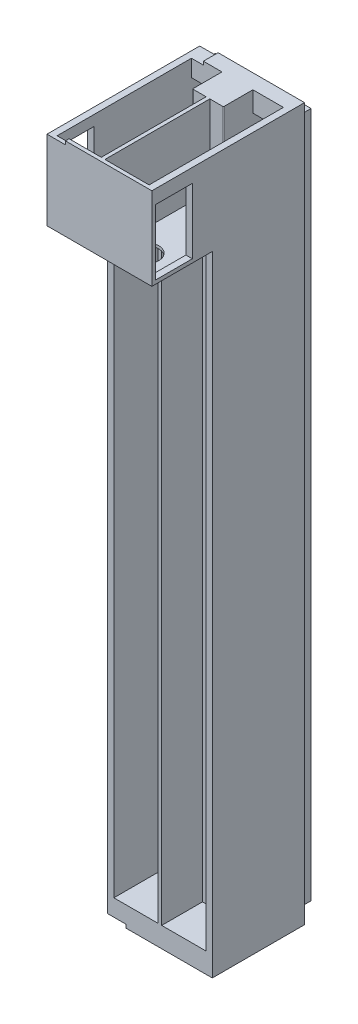
SolidWorks part; units mm, degrees
material "ABS"
ref_plane "Płaszczyzna przednia" through (0, 0, 0) normal (0, 0, 1) x (1, 0, 0)
ref_plane "Płaszczyzna górna" through (0, 0, 0) normal (0, 1, 0) x (1, 0, 0)
ref_plane "Płaszczyzna prawa" through (0, 0, 0) normal (1, 0, 0) x (0, 0, -1)
sketch "Szkic1" plane through (0, 0, 0) normal (0, 0, 1) x (1, 0, 0)
  line L0 (-90.4269, 49.2609) -> (-90.4269, -315.7391)
  line L1 (-91.9269, 53.7609) -> (-38.9269, 53.7609)
  line L2 (-91.9269, 53.7609) -> (-91.9269, -320.2391)
  line L3 (-91.9269, -320.2391) -> (-38.9269, -320.2391)
  line L4 (-38.9269, 53.7609) -> (-38.9269, -320.2391)
  line L5 (-40.4269, 49.2609) -> (-64.4269, 49.2609)
  line L6 (-90.4269, -315.7391) -> (-66.4269, -315.7391)
  line L7 (-90.4269, 49.2609) -> (-66.4269, 49.2609)
  line L8 (-66.4269, 49.2609) -> (-66.4269, -315.7391)
  line L10 (-64.4269, 49.2609) -> (-64.4269, -315.7391)
  line L13 (-40.4269, 49.2609) -> (-40.4269, -315.7391)
  line L14 (-40.4269, -315.7391) -> (-64.4269, -315.7391)
  dimension "D1" = 374
  dimension "D2" = 24
  dimension "D3" = 53
  dimension "D4" = 365
extrude "Dodanie-wyciągnięcie2" add sketch "Szkic1" along normal blind 12 contours L3 L4 L1 L2 | L6 L8 L7 L0 | L14 L10 L5 L13
sketch "Szkic2" plane through (-66.4269, 0, 0) normal (-1, 0, 0) x (0, 0, 1)
  line L0 (12, 49.2609) -> (12, -315.7391) construction
  line L1 (0, 49.2609) -> (12, 49.2609)
  line L2 (0, 49.2609) -> (0, 45.7609)
  line L3 (0, 45.7609) -> (12, 45.7609)
  line L4 (12, 49.2609) -> (12, 45.7609)
extrude "Wytnij-wyciągnięcie1" cut sketch "Szkic2" against normal blind 2
ref_plane "Płaszczyzna1" through (0, 0, 12) normal (0, 0, 1) x (1, 0, 0)
sketch "Szkic3" plane through (0, 0, 12) normal (0, 0, 1) x (1, 0, 0)
  line L6 (-38.9269, -320.2391) -> (-91.9269, -320.2391)
  line L7 (-38.9269, -320.2391) -> (-38.9269, 53.7609)
  line L8 (-38.9269, 53.7609) -> (-91.9269, 53.7609)
  line L9 (-91.9269, -320.2391) -> (-91.9269, 53.7609)
extrude "Dodanie-wyciągnięcie3" add sketch "Szkic3" along normal blind 2
sketch "Szkic4" plane through (0, 0, 14) normal (0, 0, 1) x (1, 0, 0)
  line L64 (-46.9269, -11.0391) -> (-56.3269, -11.0391)
  line L69 (-90.4269, 49.2609) -> (-40.4269, 49.2609) construction
  line L70 (-53.7269, 49.2609) -> (-40.4269, 49.2609)
  line L71 (-40.4269, 49.2609) -> (-40.4269, 18.7608)
  line L72 (-40.4269, 49.2609) -> (-40.4269, -315.7391) construction
  line L73 (-40.4269, 18.7608) -> (-53.7269, 18.7608)
  line L74 (-53.7269, 49.2609) -> (-53.7269, 18.7608)
  line L77 (-77.1269, 49.2609) -> (-77.1269, 18.7608)
  line L78 (-90.4269, 18.7608) -> (-77.1269, 18.7608)
  line L79 (-90.4269, 49.2609) -> (-90.4269, 18.7608)
  line L80 (-77.1269, 49.2609) -> (-90.4269, 49.2609)
  line L81 (-74.5269, -35.3991) -> (-74.5269, -40.4791)
  line L82 (-74.5269, -40.4791) -> (-83.9269, -40.4791)
  line L87 (-46.9269, -35.3991) -> (-46.9269, -11.0391)
  line L89 (-56.3269, -35.3991) -> (-56.3269, -11.0391)
  line L90 (-74.5269, -35.3991) -> (-74.5269, -11.0391)
  line L92 (-83.9269, -35.3991) -> (-83.9269, -11.0391)
  line L93 (-83.9269, -11.0391) -> (-74.5269, -11.0391)
  line L94 (-46.9269, -101.2391) -> (-46.9269, -166.1991)
  line L95 (-46.9269, -166.1991) -> (-56.3269, -166.1991)
  line L96 (-46.9269, -101.2391) -> (-56.3269, -101.2391)
  line L97 (-56.3269, -166.1991) -> (-56.3269, -101.2391)
  line L98 (-74.5269, -166.1991) -> (-74.5269, -101.2391)
  line L99 (-83.9269, -101.2391) -> (-74.5269, -101.2391)
  line L100 (-83.9269, -166.1991) -> (-74.5269, -166.1991)
  line L101 (-83.9269, -101.2391) -> (-83.9269, -166.1991)
  line L102 (-83.9269, -40.4791) -> (-83.9269, -35.3991)
  line L103 (-56.3269, -35.3991) -> (-56.3269, -40.4791)
  line L104 (-56.3269, -40.4791) -> (-46.9269, -40.4791)
  line L105 (-46.9269, -40.4791) -> (-46.9269, -35.3991)
extrude "Wytnij-wyciągnięcie2" cut sketch "Szkic4" against normal blind 2
sketch "Szkic5" plane through (0, 0, 14) normal (0, 0, 1) x (1, 0, 0)
  line L1 (-91.9269, -320.2391) -> (-38.9269, -320.2391) construction
  line L7 (-64.4269, -320.2391) -> (-66.4269, -320.2391)
  line L11 (-64.4269, -320.2391) -> (-64.4269, 53.7609)
  line L12 (-64.4269, 53.7609) -> (-66.4269, 53.7609)
  line L13 (-66.4269, -320.2391) -> (-66.4269, 53.7609)
extrude "Dodanie-wyciągnięcie4" add sketch "Szkic5" along normal blind 43
sketch "Szkic6" plane through (0, 0, 14) normal (0, 0, 1) x (1, 0, 0)
  line L0 (-64.4269, 16.7608) -> (-40.4269, 16.7608)
  line L4 (-64.4269, -320.2391) -> (-64.4269, 53.7609) construction
  line L5 (-40.4269, 49.2609) -> (-40.4269, -315.7391) construction
  line L6 (-40.4269, 16.7608) -> (-40.4269, 53.7609)
  line L7 (-91.9269, 53.7609) -> (-38.9269, 53.7609) construction
  line L8 (-40.4269, 53.7609) -> (-38.9269, 53.7609)
  line L19 (-90.4269, 53.7609) -> (-91.9269, 53.7609)
  line L20 (-90.4269, 16.7608) -> (-90.4269, 53.7609)
  line L21 (-66.4269, 16.7608) -> (-90.4269, 16.7608)
  line L22 (-64.4269, 16.7608) -> (-64.4269, 15.2608)
  line L23 (-64.4269, 15.2608) -> (-38.9269, 15.2608)
  line L24 (-38.9269, 15.2608) -> (-38.9269, 53.7609)
  line L25 (-91.9269, 15.2608) -> (-91.9269, 53.7609)
  line L26 (-66.4269, 15.2608) -> (-91.9269, 15.2608)
  line L27 (-66.4269, 16.7608) -> (-66.4269, 15.2608)
extrude "Dodanie-wyciągnięcie5" add sketch "Szkic6" along normal blind 41.5
ref_plane "Płaszczyzna2" through (0, 0, 55.5) normal (0, 0, 1) x (1, 0, 0)
sketch "Szkic7" plane through (0, 0, 55.5) normal (0, 0, 1) x (1, 0, 0)
  line L1 (-38.9269, 15.2608) -> (-64.4269, 15.2608)
  line L2 (-38.9269, 15.2608) -> (-38.9269, 53.7609)
  line L3 (-38.9269, 53.7609) -> (-64.4269, 53.7609)
  line L4 (-64.4269, 15.2608) -> (-64.4269, 53.7609)
  line L5 (-66.4269, 15.2608) -> (-91.9269, 15.2608)
  line L6 (-66.4269, 15.2608) -> (-66.4269, 53.7609)
  line L7 (-66.4269, 53.7609) -> (-91.9269, 53.7609)
  line L8 (-91.9269, 15.2608) -> (-91.9269, 53.7609)
extrude "Dodanie-wyciągnięcie6" add sketch "Szkic7" along normal blind 1.5
sketch "Szkic10" plane through (0, 0, 14) normal (0, 0, 1) x (1, 0, 0)
  line L0 (-91.9269, 15.2608) -> (-91.9269, -320.2391)
  line L1 (-91.9269, -320.2391) -> (-66.4269, -320.2391)
  line L2 (-66.4269, -320.2391) -> (-66.4269, -315.7391)
  line L3 (-66.4269, 15.2608) -> (-66.4269, -320.2391) construction
  line L4 (-66.4269, -315.7391) -> (-90.4269, -315.7391)
  line L5 (-90.4269, -315.7391) -> (-90.4269, 15.2608)
  line L6 (-91.9269, 15.2608) -> (-66.4269, 15.2608) construction
  line L7 (-90.4269, 15.2608) -> (-91.9269, 15.2608)
  dimension "D1" = 24
  dimension "D2" = 330.9999
extrude "Dodanie-wyciągnięcie7" add sketch "Szkic10" along normal blind 43
sketch "Szkic11" plane through (0, 0, 14) normal (0, 0, 1) x (1, 0, 0)
  line L0 (-38.9269, 15.2608) -> (-38.9269, -320.2391)
  line L1 (-38.9269, -320.2391) -> (-64.4269, -320.2391)
  line L2 (-64.4269, -320.2391) -> (-64.4269, -315.7391)
  line L3 (-64.4269, -320.2391) -> (-64.4269, 15.2608) construction
  line L4 (-64.4269, -315.7391) -> (-40.4269, -315.7391)
  line L5 (-40.4269, -315.7391) -> (-40.4269, 15.2608)
  line L6 (-64.4269, 15.2608) -> (-38.9269, 15.2608) construction
  line L7 (-40.4269, 15.2608) -> (-38.9269, 15.2608)
  dimension "D1" = 330.9999
  dimension "D2" = 24
extrude "Dodanie-wyciągnięcie8" add sketch "Szkic11" along normal blind 43
sketch "Szkic15" plane through (-91.9269, 0, 0) normal (-1, 0, 0) x (0, 0, 1)
  line L1 (57, 53.7609) -> (0, 53.7609)
  line L2 (57, 53.7609) -> (57, -320.2391)
  line L3 (57, -320.2391) -> (0, -320.2391)
  line L4 (0, 53.7609) -> (0, -320.2391)
extrude "Dodanie-wyciągnięcie10" add sketch "Szkic15" along normal blind 1
sketch "Szkic16" plane through (-38.9269, 0, 0) normal (1, 0, 0) x (0, 0, -1)
  line L1 (-57, -320.2391) -> (0, -320.2391)
  line L2 (-57, -320.2391) -> (-57, 53.7609)
  line L3 (-57, 53.7609) -> (0, 53.7609)
  line L4 (0, -320.2391) -> (0, 53.7609)
extrude "Dodanie-wyciągnięcie11" add sketch "Szkic16" along normal blind 1
sketch "Szkic17" plane through (0, 53.7609, 0) normal (0, 1, 0) x (1, 0, 0)
  line L1 (-37.9269, -57) -> (-92.9269, -57)
  line L2 (-37.9269, -57) -> (-37.9269, 0)
  line L3 (-37.9269, 0) -> (-92.9269, 0)
  line L4 (-92.9269, -57) -> (-92.9269, 0)
  line L5 (-40.4269, -55.5) -> (-64.4269, -55.5)
  line L6 (-40.4269, -55.5) -> (-40.4269, -14)
  line L7 (-40.4269, -14) -> (-64.4269, -14)
  line L8 (-64.4269, -55.5) -> (-64.4269, -14)
  line L9 (-66.4269, -55.5) -> (-90.4269, -55.5)
  line L10 (-66.4269, -55.5) -> (-66.4269, -14)
  line L11 (-66.4269, -14) -> (-90.4269, -14)
  line L12 (-90.4269, -55.5) -> (-90.4269, -14)
extrude "Dodanie-wyciągnięcie12" add sketch "Szkic17" along normal blind 1
sketch "Szkic18" plane through (0, -320.2391, 0) normal (0, -1, 0) x (1, 0, 0)
  line L1 (-92.9269, 57) -> (-37.9269, 57)
  line L2 (-92.9269, 57) -> (-92.9269, 0)
  line L3 (-92.9269, 0) -> (-37.9269, 0)
  line L4 (-37.9269, 57) -> (-37.9269, 0)
extrude "Dodanie-wyciągnięcie13" add sketch "Szkic18" along normal blind 1
sketch "Szkic19" plane through (0, 0, 0) normal (0, 0, -1) x (-1, 0, 0)
  line L1 (37.9269, -321.2391) -> (92.9269, -321.2391)
  line L2 (37.9269, -321.2391) -> (37.9269, 54.7609)
  line L3 (37.9269, 54.7609) -> (92.9269, 54.7609)
  line L4 (92.9269, -321.2391) -> (92.9269, 54.7609)
  line L8 (91.4269, -319.7391) -> (39.4269, -319.7391)
  line L9 (91.4269, -319.7391) -> (91.4269, 53.2609)
  line L10 (91.4269, 53.2609) -> (39.4269, 53.2609)
  line L11 (39.4269, -319.7391) -> (39.4269, 53.2609)
extrude "Wytnij-wyciągnięcie7" cut sketch "Szkic19" against normal blind 6
sketch "Szkic23" plane through (0, 0, 57) normal (0, 0, 1) x (1, 0, 0)
  line L6 (-40.4269, 54.7609) -> (-64.4269, 54.7609)
  line L16 (-40.4269, 16.7608) -> (-64.4269, 16.7608)
  line L17 (-64.4269, 54.7609) -> (-64.4269, 16.7608)
  line L18 (-40.4269, 16.7608) -> (-40.4269, 54.7609)
  line L21 (-90.4269, 16.7608) -> (-66.4269, 16.7608)
  line L22 (-90.4269, 16.7608) -> (-90.4269, 54.7609)
  line L23 (-66.4269, 54.7609) -> (-66.4269, 16.7608)
  line L24 (-90.4269, 54.7609) -> (-66.4269, 54.7609)
extrude "Wytnij-wyciągnięcie11" cut sketch "Szkic23" against normal blind 10
sketch "Szkic24" plane through (0, 0, 57) normal (0, 0, 1) x (1, 0, 0)
  line L0 (-40.4269, 54.7609) -> (-37.9269, 54.7609)
  line L1 (-37.9269, 15.2608) -> (-92.9269, 15.2608)
  line L2 (-37.9269, 54.7609) -> (-37.9269, -321.2391) construction
  line L3 (-37.9269, 15.2608) -> (-37.9269, 54.7609)
  line L4 (-92.9269, -321.2391) -> (-92.9269, 54.7609) construction
  line L5 (-92.9269, 15.2608) -> (-92.9269, 54.7609)
  line L6 (-92.9269, 54.7609) -> (-90.4269, 54.7609)
  line L7 (-90.4269, 54.7609) -> (-90.4269, 16.7608)
  line L8 (-90.4269, 16.7608) -> (-66.4269, 16.7608)
  line L9 (-66.4269, 16.7608) -> (-66.4269, 54.7609)
  line L10 (-66.4269, 54.7609) -> (-64.4269, 54.7609)
  line L11 (-64.4269, 54.7609) -> (-64.4269, 16.7608)
  line L12 (-64.4269, 16.7608) -> (-40.4269, 16.7608)
  line L13 (-40.4269, 16.7608) -> (-40.4269, 54.7609)
extrude "Dodanie-wyciągnięcie14" add sketch "Szkic24" along normal blind 32
sketch "Szkic25" plane through (0, 16.7608, 0) normal (0, 1, 0) x (1, 0, 0)
  line L0 (-64.4269, -89) -> (-64.4269, -14) construction
  line L1 (-40.4269, -89) -> (-64.4269, -89)
  line L2 (-40.4269, -89) -> (-40.4269, -87)
  line L3 (-40.4269, -87) -> (-64.4269, -87)
  line L4 (-64.4269, -89) -> (-64.4269, -87)
extrude "Dodanie-wyciągnięcie15" add sketch "Szkic25" along normal blind 38
sketch "Szkic26" plane through (0, 16.7608, 0) normal (0, 1, 0) x (1, 0, 0)
  line L0 (-90.4269, -89) -> (-90.4269, -14) construction
  line L1 (-66.4269, -89) -> (-90.4269, -89)
  line L2 (-66.4269, -89) -> (-66.4269, -87)
  line L3 (-66.4269, -87) -> (-90.4269, -87)
  line L4 (-90.4269, -89) -> (-90.4269, -87)
extrude "Dodanie-wyciągnięcie16" add sketch "Szkic26" along normal blind 38
sketch "Szkic27" plane through (0, 15.2608, 0) normal (0, -1, 0) x (1, 0, 0)
  circle A9 centre (-78.1769, 76.5) radius 7
  circle A10 centre (-52.6769, 76.5) radius 7
  dimension "D2" = 14
extrude "Wytnij-wyciągnięcie12" cut sketch "Szkic27" against normal blind 10
sketch "Szkic28" plane through (-37.9269, 0, 0) normal (1, 0, 0) x (0, 0, -1)
  line L7 (-87, 17.2608) -> (-67, 17.2608)
  line L8 (-87, 17.2608) -> (-87, 52.7608)
  line L9 (-87, 52.7608) -> (-67, 52.7608)
  line L10 (-67, 17.2608) -> (-67, 52.7608)
  dimension "D1" = 20
extrude "Wytnij-wyciągnięcie13" cut sketch "Szkic28" against normal blind 3
sketch "Szkic29" plane through (-92.9269, 0, 0) normal (-1, 0, 0) x (0, 0, 1)
  line L7 (87, 52.7608) -> (67, 52.7608)
  line L8 (87, 52.7608) -> (87, 17.2608)
  line L9 (87, 17.2608) -> (67, 17.2608)
  line L10 (67, 52.7608) -> (67, 17.2608)
extrude "Wytnij-wyciągnięcie14" cut sketch "Szkic29" against normal blind 3
sketch "Szkic33" plane through (0, 54.7609, 0) normal (0, 1, 0) x (1, 0, 0)
  line L1 (-37.9269, -89) -> (-92.9269, -89)
  line L2 (-37.9269, -89) -> (-37.9269, -6)
  line L3 (-37.9269, -6) -> (-92.9269, -6)
  line L4 (-92.9269, -89) -> (-92.9269, -6)
  line L5 (-64.4269, -14) -> (-40.4269, -14)
  line L6 (-64.4269, -14) -> (-64.4269, -87)
  line L7 (-64.4269, -87) -> (-40.4269, -87)
  line L8 (-40.4269, -14) -> (-40.4269, -87)
  line L9 (-90.4269, -14) -> (-66.4269, -14)
  line L10 (-90.4269, -14) -> (-90.4269, -87)
  line L11 (-90.4269, -87) -> (-66.4269, -87)
  line L12 (-66.4269, -14) -> (-66.4269, -87)
extrude "Dodanie-wyciągnięcie17" add sketch "Szkic33" along normal blind 5.5
sketch "Szkic34" plane through (0, -321.2391, 0) normal (0, -1, 0) x (1, 0, 0)
  line L1 (-92.9269, 57) -> (-37.9269, 57)
  line L2 (-92.9269, 57) -> (-92.9269, 6)
  line L3 (-92.9269, 6) -> (-37.9269, 6)
  line L4 (-37.9269, 57) -> (-37.9269, 6)
extrude "Dodanie-wyciągnięcie18" add sketch "Szkic34" along normal blind 5.5
sketch "Szkic35" plane through (-92.9269, 0, 0) normal (-1, 0, 0) x (0, 0, 1)
  line L0 (89, 60.2609) -> (89, 15.2608)
  line L1 (89, 15.2608) -> (57, 15.2608)
  line L2 (57, 15.2608) -> (57, -326.7391)
  line L3 (57, -326.7391) -> (6, -326.7391)
  line L4 (6, -326.7391) -> (6, 60.2609)
  line L5 (6, 60.2609) -> (89, 60.2609)
  line L7 (87, 52.7608) -> (67, 52.7608)
  line L8 (87, 52.7608) -> (87, 17.2608)
  line L9 (87, 17.2608) -> (67, 17.2608)
  line L10 (67, 52.7608) -> (67, 17.2608)
extrude "Dodanie-wyciągnięcie19" add sketch "Szkic35" along normal blind 1
sketch "Szkic36" plane through (-37.9269, 0, 0) normal (1, 0, 0) x (0, 0, -1)
  line L0 (-57, -326.7391) -> (-57, 15.2608)
  line L1 (-57, 15.2608) -> (-89, 15.2608)
  line L2 (-89, 15.2608) -> (-89, 60.2609)
  line L3 (-89, 60.2609) -> (-6, 60.2609)
  line L4 (-6, 60.2609) -> (-6, -326.7391)
  line L5 (-6, -326.7391) -> (-57, -326.7391)
  line L7 (-67, 52.7608) -> (-87, 52.7608)
  line L8 (-67, 52.7608) -> (-67, 17.2608)
  line L9 (-67, 17.2608) -> (-87, 17.2608)
  line L10 (-87, 52.7608) -> (-87, 17.2608)
extrude "Dodanie-wyciągnięcie20" add sketch "Szkic36" along normal blind 1
sketch "Szkic37" plane through (0, 0, 14) normal (0, 0, 1) x (1, 0, 0)
  line L1 (-64.4269, -315.7391) -> (-40.4269, -315.7391)
  line L2 (-64.4269, -315.7391) -> (-64.4269, 15.2608)
  line L3 (-64.4269, 15.2608) -> (-40.4269, 15.2608)
  line L4 (-40.4269, -315.7391) -> (-40.4269, 15.2608)
extrude "Wytnij-wyciągnięcie15" cut sketch "Szkic37" against normal blind 2
sketch "Szkic38" plane through (0, 0, 14) normal (0, 0, 1) x (1, 0, 0)
  line L1 (-90.4269, -315.7391) -> (-66.4269, -315.7391)
  line L2 (-90.4269, -315.7391) -> (-90.4269, 15.2608)
  line L3 (-90.4269, 15.2608) -> (-66.4269, 15.2608)
  line L4 (-66.4269, -315.7391) -> (-66.4269, 15.2608)
extrude "Wytnij-wyciągnięcie16" cut sketch "Szkic38" against normal blind 2
sketch "Szkic39" plane through (0, 0, 12) normal (0, 0, -1) x (-1, 0, 0)
  line L0 (90.4269, 15.2608) -> (66.4269, 15.2608)
  line L1 (66.4269, 15.2608) -> (66.4269, 45.7609)
  line L2 (66.4269, 45.7609) -> (64.4269, 45.7609)
  line L3 (64.4269, 45.7609) -> (64.4269, 15.2608)
  line L4 (64.4269, 15.2608) -> (40.4269, 15.2608)
  line L5 (40.4269, 15.2608) -> (40.4269, 49.2609)
  line L6 (40.4269, 49.2609) -> (90.4269, 49.2609)
  line L7 (90.4269, 49.2609) -> (90.4269, 15.2608)
extrude "Wytnij-wyciągnięcie17" cut sketch "Szkic39" against normal blind 2
sketch "Szkic40" plane through (0, 0, 14) normal (0, 0, -1) x (-1, 0, 0)
  line L1 (64.4269, 49.2609) -> (66.4269, 49.2609)
  line L2 (64.4269, 49.2609) -> (64.4269, 45.7609)
  line L3 (64.4269, 45.7609) -> (66.4269, 45.7609)
  line L4 (66.4269, 49.2609) -> (66.4269, 45.7609)
extrude "Wytnij-wyciągnięcie18" cut sketch "Szkic40" against normal blind 14
sketch "Szkic41" plane through (0, -315.7391, 0) normal (0, 1, 0) x (1, 0, 0)
  line L2 (-52.4269, -32) -> (-40.4269, -32)
  line L3 (-40.4269, -57) -> (-40.4269, 0) construction
  line L4 (-52.4269, -32) -> (-64.4269, -32)
  line L5 (-64.4269, -57) -> (-64.4269, 0) construction
  line L6 (-64.4269, -32) -> (-64.4269, -34)
  line L7 (-64.4269, -34) -> (-40.4269, -34)
  line L8 (-40.4269, -34) -> (-40.4269, -32)
extrude "Dodanie-wyciągnięcie21" add sketch "Szkic41" along normal blind 331
sketch "Szkic42" plane through (0, 0, 34) normal (0, 0, 1) x (1, 0, 0)
  line L4 (-55.6269, 15.2608) -> (-45.6269, 15.2608)
  line L5 (-55.6269, 15.2608) -> (-55.6269, -309.7391)
  line L9 (-40.4269, 15.2608) -> (-64.4269, 15.2608) construction
  line L11 (-55.6269, -309.7391) -> (-45.6269, -309.7391)
  line L12 (-45.6269, 15.2608) -> (-45.6269, -309.7391)
extrude "Wytnij-wyciągnięcie19" cut sketch "Szkic42" against normal blind 2
sketch "Szkic43" plane through (0, 0, 32) normal (0, 0, -1) x (-1, 0, 0)
  line L15 (45.6269, 15.2608) -> (45.6269, -309.7391)
  line L16 (45.6269, -309.7391) -> (55.6269, -309.7391)
  line L17 (55.6269, -309.7391) -> (55.6269, 15.2608)
  line L18 (55.6269, 15.2608) -> (57.6269, 15.2608)
  line L19 (64.4269, 15.2608) -> (55.6269, 15.2608) construction
  line L20 (57.6269, 15.2608) -> (57.6269, -311.7392)
  line L25 (45.6269, 15.2608) -> (43.6269, 15.2608)
  line L26 (45.6269, 15.2608) -> (40.4269, 15.2608) construction
  line L27 (43.6269, 15.2608) -> (43.6269, -311.7392)
  line L28 (43.6269, -311.7392) -> (57.6269, -311.7392)
extrude "Dodanie-wyciągnięcie22" add sketch "Szkic43" along normal blind 18
sketch "Szkic44" plane through (0, 0, 14) normal (0, 0, -1) x (-1, 0, 0)
  line L12 (64.4269, 16.7608) -> (40.4269, 16.7608)
  line L13 (40.4269, 16.7608) -> (40.4269, 15.2608)
  line L14 (40.4269, 15.2608) -> (43.6269, 15.2608)
  line L15 (43.6269, 15.2608) -> (43.6269, -311.7392)
  line L16 (43.6269, -311.7392) -> (57.6269, -311.7392)
  line L17 (57.6269, -311.7392) -> (57.6269, 15.2608)
  line L18 (57.6269, 15.2608) -> (64.4269, 15.2608)
  line L19 (64.4269, 15.2608) -> (64.4269, 16.7608)
  line L21 (55.6269, 15.2608) -> (45.6269, 15.2608)
  line L22 (55.6269, 15.2608) -> (55.6269, -309.7391)
  line L23 (55.6269, -309.7391) -> (45.6269, -309.7391)
  line L24 (45.6269, 15.2608) -> (45.6269, -309.7391)
extrude "Dodanie-wyciągnięcie23" add sketch "Szkic44" along normal blind 10
sketch "Szkic45" plane through (-64.4269, 0, 0) normal (1, 0, 0) x (0, 0, -1)
  line L0 (-28, 60.2609) -> (-28, 16.7608)
  line L1 (-14, 60.2609) -> (-87, 60.2609) construction
  line L2 (-87, 16.7608) -> (-4, 16.7608) construction
  line L3 (-28, 16.7608) -> (-30, 16.7608)
  line L4 (-30, 16.7608) -> (-30, 60.2609)
  line L5 (-30, 60.2609) -> (-28, 60.2609)
extrude "Dodanie-wyciągnięcie24" add sketch "Szkic45" along normal blind 7.4
sketch "Szkic46" plane through (0, 0, 14) normal (0, 0, 1) x (1, 0, 0)
  line L0 (-64.4269, 60.2609) -> (-57.0269, 60.2609)
  line L1 (-40.4269, 60.2609) -> (-64.4269, 60.2609) construction
  line L2 (-57.0269, 60.2609) -> (-57.0269, 49.2609)
  line L3 (-40.4269, 49.2609) -> (-64.4269, 49.2609) construction
  line L4 (-57.0269, 49.2609) -> (-64.4269, 49.2609)
  line L5 (-64.4269, 49.2609) -> (-64.4269, 60.2609)
extrude "Dodanie-wyciągnięcie25" add sketch "Szkic46" along normal blind 14
sketch "Szkic47" plane through (0, 0, 28) normal (0, 0, -1) x (-1, 0, 0)
  line L0 (57.0269, 49.2609) -> (59.0269, 49.2609)
  line L1 (90.4269, 49.2609) -> (40.4269, 49.2609) construction
  line L2 (59.0269, 49.2609) -> (59.0269, 16.7608)
  line L3 (57.0269, 16.7608) -> (64.4269, 16.7608) construction
  line L4 (59.0269, 16.7608) -> (57.0269, 16.7608)
  line L5 (57.0269, 16.7608) -> (57.0269, 49.2609)
extrude "Dodanie-wyciągnięcie26" add sketch "Szkic47" along normal blind 24
sketch "Szkic48" plane through (0, 60.2609, 0) normal (0, 1, 0) x (1, 0, 0)
  line L0 (-93.9269, -6) -> (-83.9269, -6)
  line L1 (-36.9269, -6) -> (-93.9269, -6) construction
  line L2 (-83.9269, -6) -> (-83.9269, -14)
  line L3 (-66.4269, -14) -> (-90.4269, -14) construction
  line L4 (-83.9269, -14) -> (-90.4269, -14)
  line L5 (-90.4269, -14) -> (-90.4269, -87)
  line L6 (-90.4269, -87) -> (-83.9269, -87)
  line L7 (-90.4269, -87) -> (-66.4269, -87) construction
  line L8 (-83.9269, -87) -> (-83.9269, -89)
  line L9 (-93.9269, -89) -> (-36.9269, -89) construction
  line L10 (-83.9269, -89) -> (-93.9269, -89)
  line L11 (-93.9269, -89) -> (-93.9269, -6)
extrude "Wytnij-wyciągnięcie20" cut sketch "Szkic48" against normal blind 1.85
sketch "Szkic49" plane through (0, -326.7391, 0) normal (0, -1, 0) x (1, 0, 0)
  line L0 (-93.9269, 57) -> (-83.9269, 57)
  line L1 (-36.9269, 57) -> (-93.9269, 57) construction
  line L2 (-83.9269, 57) -> (-83.9269, 6)
  line L3 (-93.9269, 6) -> (-36.9269, 6) construction
  line L4 (-83.9269, 6) -> (-93.9269, 6)
  line L5 (-93.9269, 6) -> (-93.9269, 57)
extrude "Wytnij-wyciągnięcie21" cut sketch "Szkic49" against normal blind 1.85
sketch "Szkic50" plane through (0, 0, 57) normal (0, 0, 1) x (1, 0, 0)
  line L0 (-40.4269, 15.2608) -> (-36.9269, 15.2608)
  line L1 (-36.9269, 15.2608) -> (-36.9269, -326.7391)
  line L2 (-36.9269, -326.7391) -> (-83.9269, -326.7391)
  line L3 (-83.9269, -326.7391) -> (-83.9269, -324.8891)
  line L4 (-83.9269, -324.8891) -> (-93.9269, -324.8891)
  line L5 (-93.9269, -324.8891) -> (-93.9269, 15.2608)
  line L6 (-93.9269, 15.2608) -> (-90.4269, 15.2608)
  line L7 (-90.4269, 15.2608) -> (-90.4269, -315.7391)
  line L8 (-90.4269, -315.7391) -> (-66.4269, -315.7391)
  line L9 (-66.4269, -315.7391) -> (-66.4269, 15.2608)
  line L10 (-66.4269, 15.2608) -> (-64.4269, 15.2608)
  line L11 (-64.4269, 15.2608) -> (-64.4269, -315.7391)
  line L12 (-64.4269, -315.7391) -> (-40.4269, -315.7391)
  line L13 (-40.4269, -315.7391) -> (-40.4269, 15.2608)
extrude "Wytnij-wyciągnięcie22" cut sketch "Szkic50" against normal blind 0.85
sketch "Szkic51" plane through (-66.4269, 0, 0) normal (-1, 0, 0) x (0, 0, 1)
  line L0 (28, 45.7609) -> (28, 16.7608)
  line L1 (87, 16.7608) -> (14, 16.7608) construction
  line L2 (28, 16.7608) -> (30, 16.7608)
  line L3 (30, 16.7608) -> (30, 60.2609)
  line L4 (87, 60.2609) -> (14, 60.2609) construction
  line L5 (30, 60.2609) -> (28, 60.2609)
  line L6 (28, 60.2609) -> (28, 45.7609)
extrude "Dodanie-wyciągnięcie27" add sketch "Szkic51" along normal blind 7.4
sketch "Szkic52" plane through (0, 0, 14) normal (0, 0, 1) x (1, 0, 0)
  line L0 (-66.4269, 60.2609) -> (-73.8269, 60.2609)
  line L1 (-66.4269, 60.2609) -> (-83.9269, 60.2609) construction
  line L2 (-73.8269, 60.2609) -> (-73.8269, 49.2609)
  line L3 (-66.4269, 49.2609) -> (-90.4269, 49.2609) construction
  line L4 (-73.8269, 49.2609) -> (-66.4269, 49.2609)
  line L5 (-66.4269, 49.2609) -> (-66.4269, 60.2609)
extrude "Dodanie-wyciągnięcie28" add sketch "Szkic52" along normal blind 14
sketch "Szkic53" plane through (0, 0, 28) normal (0, 0, -1) x (-1, 0, 0)
  line L0 (73.8269, 16.7608) -> (71.8269, 16.7608)
  line L1 (66.4269, 16.7608) -> (90.4269, 16.7608) construction
  line L2 (71.8269, 16.7608) -> (71.8269, 49.2609)
  line L3 (90.4269, 49.2609) -> (40.4269, 49.2609) construction
  line L4 (71.8269, 49.2609) -> (73.8269, 49.2609)
  line L5 (73.8269, 49.2609) -> (59.0269, 49.2609) construction
  line L6 (73.8269, 49.2609) -> (73.8269, 16.7608)
extrude "Dodanie-wyciągnięcie30" add sketch "Szkic53" along normal blind 24
sketch "Szkic54" plane through (0, 0, 14) normal (0, 0, -1) x (-1, 0, 0)
  line L1 (66.4269, 16.7608) -> (90.4269, 16.7608)
  line L2 (66.4269, 16.7608) -> (66.4269, 15.2608)
  line L3 (66.4269, 15.2608) -> (90.4269, 15.2608)
  line L4 (90.4269, 16.7608) -> (90.4269, 15.2608)
extrude "Dodanie-wyciągnięcie31" add sketch "Szkic54" along normal blind 10
fillet "Zaokrąglenie1" radius 0.5 1 edges at (-73.8269, 38.5109, 30)
fillet "Zaokrąglenie2" radius 0.5 1 edges at (-57.0269, 38.5109, 30)
